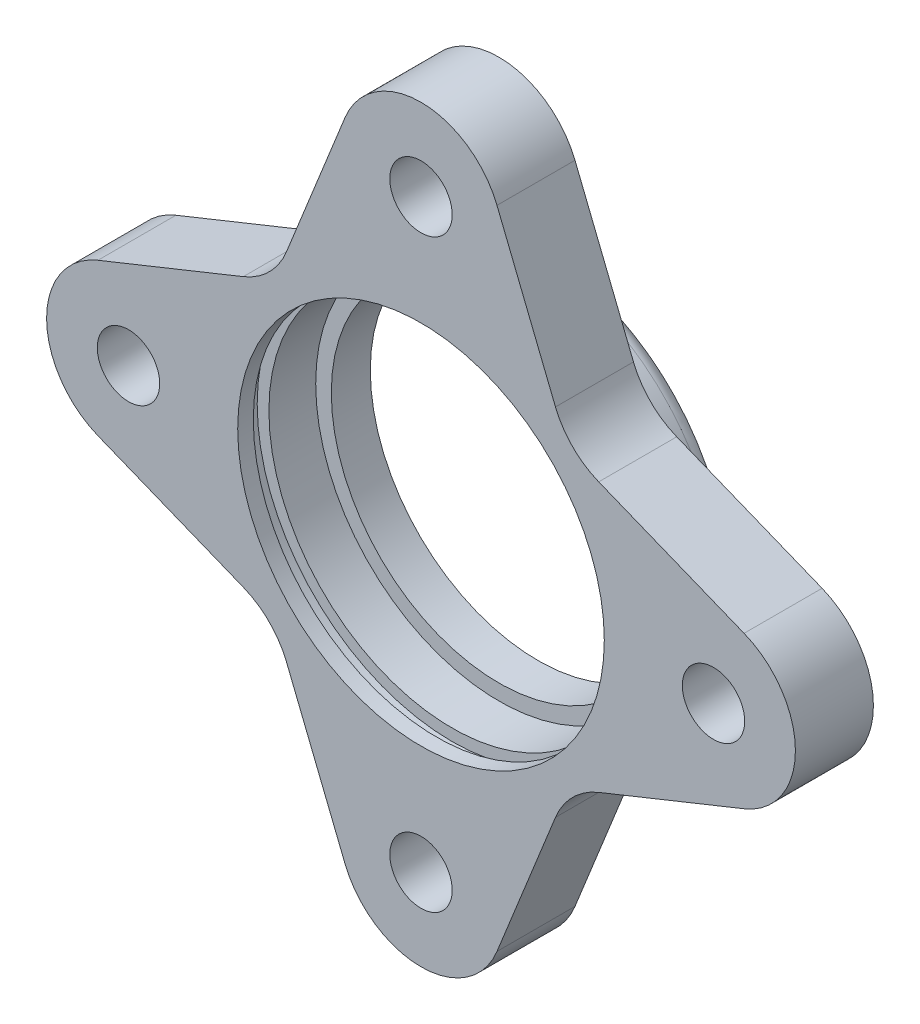
SolidWorks part; units mm, degrees
ref_plane "Front Plane" through (0, 0, 0) normal (0, 0, 1) x (1, 0, 0)
ref_plane "Top Plane" through (0, 0, 0) normal (0, 1, 0) x (1, 0, 0)
ref_plane "Right Plane" through (0, 0, 0) normal (1, 0, 0) x (0, 0, -1)
sketch "Sketch1" plane through (0, 0, 0) normal (0, 0, 1) x (1, 0, 0)
  circle A0 centre (0, 0) radius 23.5
  circle A1 centre (0, 0) radius 37.5
  circle A2 centre (0, 0) radius 48
  circle A3 centre (37.5, 0) radius 4
  circle A4 centre (0, 37.5) radius 4
  circle A5 centre (-37.5, 0) radius 4
  circle A6 centre (0, -37.5) radius 4
  dimension "D1" = 47
  dimension "D2" = 75
  dimension "D3" = 96
  dimension "D4" = 8
  dimension "D5" = 8
  dimension "D6" = 8
  dimension "D7" = 8
extrude "Boss-Extrude1" add sketch "Sketch1" along normal blind 10 contours A2 A6 A1 A5 A4 A3 | A6 A1 A3 A4 A5 A0
sketch "Sketch2" plane through (0, 0, 10) normal (0, 0, 1) x (1, 0, 0)
  circle A0 centre (0, 0) radius 23.5
  circle A1 centre (0, 0) radius 25
  dimension "D1" = 50
extrude "Cut-Extrude3" cut sketch "Sketch2" against normal blind 2 from offset 2 offset against normal yes
sketch "Sketch3" plane through (0, 0, 0) normal (0, 0, -1) x (-1, 0, 0)
  line L0 (0, 0) -> (0, 72.9758) construction
  line L1 (0, 0) -> (-26.5165, 26.5165) construction
  line L2 (-9.7411, 41.4194) -> (-17.2393, 22.7837)
  line L3 (-41.4194, 9.7411) -> (-22.7837, 17.2393)
  circle A0 centre (0, 0) radius 37.5
  arc A1 (0, 48) -> (-9.7411, 41.4194) centre (0, 37.5) ccw
  arc A2 (-22.7837, 17.2393) -> (-17.2393, 22.7837) centre (-26.5165, 26.5165) ccw
  arc A3 (-41.4194, 9.7411) -> (-48, 0) centre (-37.5, 0) ccw
  arc A4 (0, 48) -> (-48, 0) centre (0, 0) ccw
  circle M14 centre (0, 0) radius 48
extrude "Cut-Extrude4" cut sketch "Sketch3" against normal through all contours A3 L3 A0 L2 A1 M14 | L3 A2 L2 A0
pattern_circular "CirPattern4" count 4 over 360 about axis through (0, 0, 0) along (0, 0, 1) of "Cut-Extrude4"
sketch "Sketch4" plane through (0, 0, 0) normal (0, 0, -1) x (-1, 0, 0)
  circle A0 centre (0, 0) radius 21.5
  circle A1 centre (0, 0) radius 25.5
  dimension "D1" = 51
  dimension "D2" = 43
extrude "Boss-Extrude2" add sketch "Sketch4" along normal blind 5
fillet "Fillet1" radius 2 1 edges at (-25.5, 0, -5)
fillet "Fillet2" radius 1 1 edges at (25.5, 0, 0)
sketch "Sketch5" plane through (0, 0, 10) normal (0, 0, 1) x (1, 0, 0)
  line L0 (9.7411, 41.4194) -> (17.2393, 22.7837) construction
  line L1 (41.4194, 9.7411) -> (22.7837, 17.2393) construction
  line L2 (41.4194, -9.7411) -> (22.7837, -17.2393) construction
  line L3 (9.7411, -41.4194) -> (17.2393, -22.7837) construction
  line L4 (-9.7411, -41.4194) -> (-17.2393, -22.7837) construction
  line L5 (-41.4194, -9.7411) -> (-22.7837, -17.2393) construction
  line L6 (-41.4194, 9.7411) -> (-22.7837, 17.2393) construction
  line L7 (-9.7411, 41.4194) -> (-17.2393, 22.7837) construction
  line L8 (9.7411, 41.4194) -> (17.2393, 22.7837)
  line L9 (41.4194, 9.7411) -> (22.7837, 17.2393)
  line L10 (41.4194, -9.7411) -> (22.7837, -17.2393)
  line L11 (9.7411, -41.4194) -> (17.2393, -22.7837)
  line L12 (-9.7411, -41.4194) -> (-17.2393, -22.7837)
  line L13 (-41.4194, -9.7411) -> (-22.7837, -17.2393)
  line L14 (-41.4194, 9.7411) -> (-22.7837, 17.2393)
  line L15 (-9.7411, 41.4194) -> (-17.2393, 22.7837)
  arc A0 (17.2393, 22.7837) -> (22.7837, 17.2393) centre (26.5165, 26.5165) ccw construction
  arc A1 (41.4194, -9.7411) -> (41.4194, 9.7411) centre (37.5, 0) ccw construction
  arc A2 (22.7837, -17.2393) -> (17.2393, -22.7837) centre (26.5165, -26.5165) ccw construction
  arc A3 (-9.7411, -41.4194) -> (9.7411, -41.4194) centre (0, -37.5) ccw construction
  arc A4 (-17.2393, -22.7837) -> (-22.7837, -17.2393) centre (-26.5165, -26.5165) ccw construction
  arc A5 (-41.4194, 9.7411) -> (-41.4194, -9.7411) centre (-37.5, 0) ccw construction
  arc A6 (-22.7837, 17.2393) -> (-17.2393, 22.7837) centre (-26.5165, 26.5165) ccw construction
  arc A7 (9.7411, 41.4194) -> (-9.7411, 41.4194) centre (0, 37.5) ccw construction
  arc A8 (17.2393, 22.7837) -> (22.7837, 17.2393) centre (26.5165, 26.5165) ccw
  arc A9 (41.4194, -9.7411) -> (41.4194, 9.7411) centre (37.5, 0) ccw
  arc A10 (22.7837, -17.2393) -> (17.2393, -22.7837) centre (26.5165, -26.5165) ccw
  arc A11 (-9.7411, -41.4194) -> (9.7411, -41.4194) centre (0, -37.5) ccw
  arc A12 (-17.2393, -22.7837) -> (-22.7837, -17.2393) centre (-26.5165, -26.5165) ccw
  arc A13 (-41.4194, 9.7411) -> (-41.4194, -9.7411) centre (-37.5, 0) ccw
  arc A14 (-22.7837, 17.2393) -> (-17.2393, 22.7837) centre (-26.5165, 26.5165) ccw
  arc A15 (9.7411, 41.4194) -> (-9.7411, 41.4194) centre (0, 37.5) ccw
